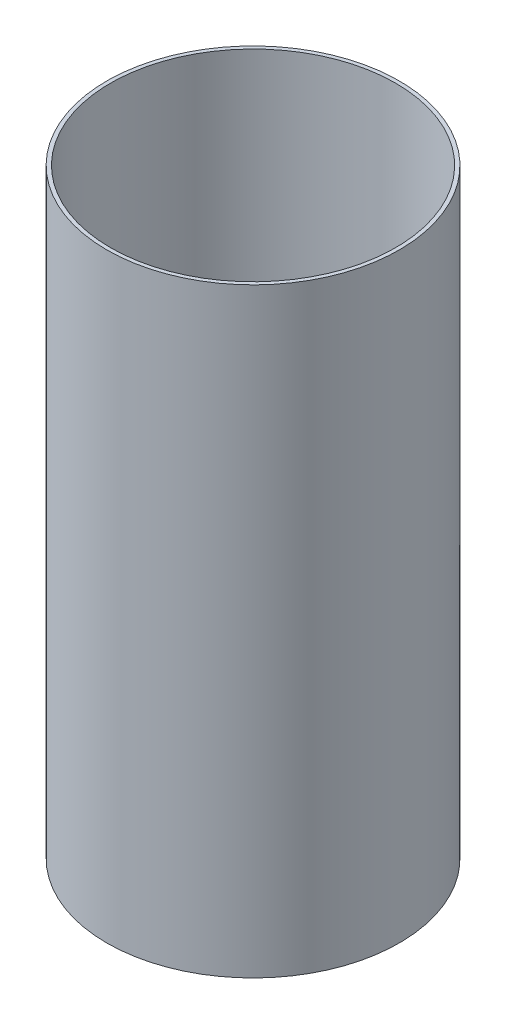
SolidWorks part; units mm, degrees
material "A-Glass Fiber"
ref_plane "Front Plane" through (0, 0, 0) normal (0, 0, 1) x (1, 0, 0)
ref_plane "Top Plane" through (0, 0, 0) normal (0, 1, 0) x (1, 0, 0)
ref_plane "Right Plane" through (0, 0, 0) normal (1, 0, 0) x (0, 0, -1)
sketch "Sketch1" plane through (0, 0, 0) normal (0, 1, 0) x (1, 0, 0)
  circle A0 centre (0, 0) radius 49.53
  circle A1 centre (0, 0) radius 48.26
  dimension "D1" = 99.06
  dimension "D2" = 96.52
extrude "Boss-Extrude1" add sketch "Sketch1" along normal blind 203.2 contours A1 | A0
equation "\"Length\"=8"
equation "\"D1@Boss-Extrude1\"=\"Length\""
